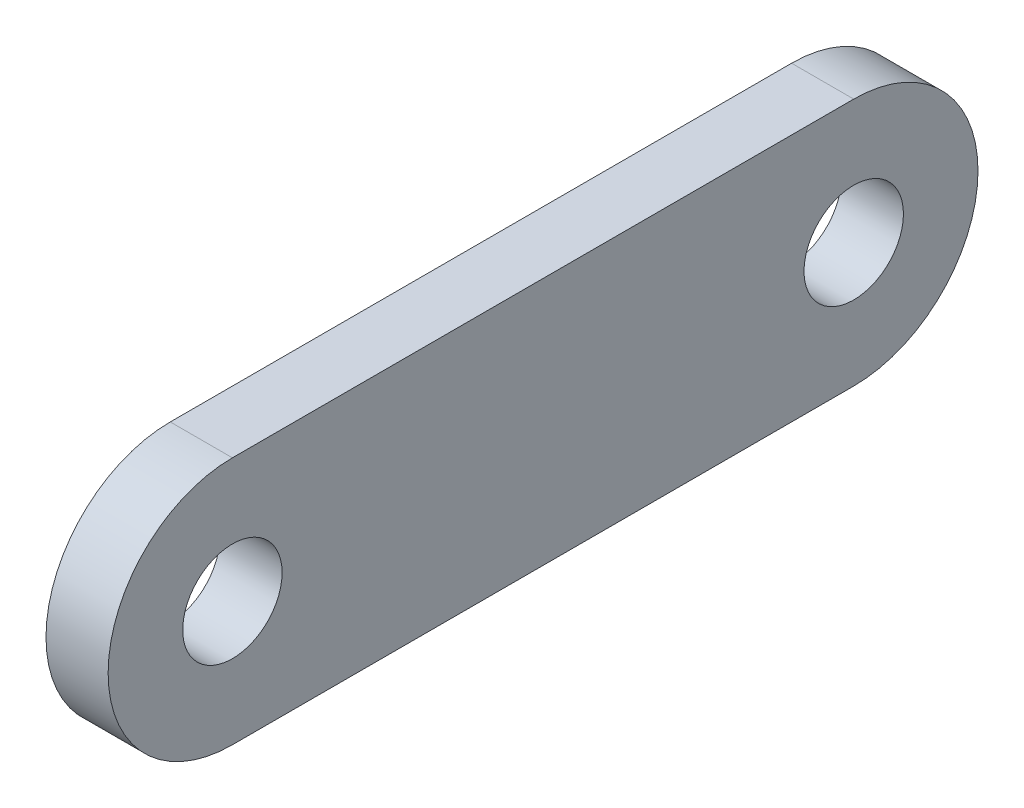
SolidWorks part; units mm, degrees
material "6061-T6 (SS)"
ref_plane "Front Plane" through (0, 0, 0) normal (0, 0, 1) x (1, 0, 0)
ref_plane "Top Plane" through (0, 0, 0) normal (0, 1, 0) x (1, 0, 0)
ref_plane "Right Plane" through (0, 0, 0) normal (1, 0, 0) x (0, 0, -1)
sketch "Sketch1" plane through (0, 0, 0) normal (1, 0, 0) x (0, 0, -1)
  line L0 (-25, 0) -> (25, 0) construction
  line L1 (-25, 10) -> (25, 10)
  line L2 (-25, -10) -> (25, -10)
  arc A0 (-25, 10) -> (-25, -10) centre (-25, 0) ccw
  arc A1 (25, -10) -> (25, 10) centre (25, 0) ccw
  point P3 (0, 0)
  dimension "D1" = 50
  dimension "D2" = 20
extrude "Boss-Extrude1" add sketch "Sketch1" along normal blind 5
sketch "Sketch2" plane through (5, 0, 0) normal (1, 0, 0) x (0, 0, -1)
  circle A0 centre (-25, 0) radius 4
  circle A1 centre (25, 0) radius 4
  arc A3 (-25, 10) -> (-25, -10) centre (-25, 0) ccw construction
  arc A4 (25, -10) -> (25, 10) centre (25, 0) ccw construction
  dimension "D1" = 8
extrude "Cut-Extrude1" cut sketch "Sketch2" against normal through all
sketch "Sketch3" plane through (5, 0, 0) normal (1, 0, 0) x (0, 0, -1)
  line L1 (-38.3474, 17.5661) -> (41.6526, 17.5661)
  line L2 (-38.3474, 17.5661) -> (-38.3474, -12.4339)
  line L3 (-38.3474, -12.4339) -> (41.6526, -12.4339)
  line L4 (41.6526, 17.5661) -> (41.6526, -12.4339)
  dimension "D1" = 80
  dimension "D2" = 30
